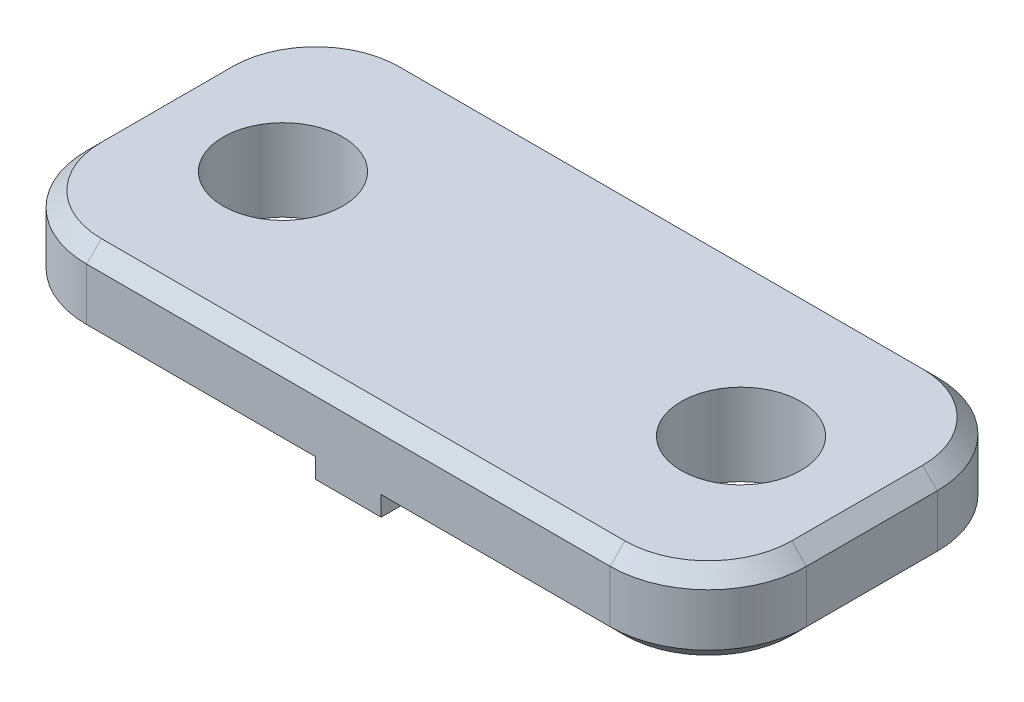
SolidWorks part; units mm, degrees
ref_plane "Front Plane" through (0, 0, 0) normal (0, 0, 1) x (1, 0, 0)
ref_plane "Top Plane" through (0, 0, 0) normal (0, 1, 0) x (1, 0, 0)
ref_plane "Right Plane" through (0, 0, 0) normal (1, 0, 0) x (0, 0, -1)
sketch "Sketch1" plane through (0, 0, 0) normal (0, 1, 0) x (1, 0, 0)
  line L1 (-11, -5) -> (11, -5)
  line L2 (-11, -5) -> (-11, 5)
  line L3 (-11, 5) -> (11, 5)
  line L4 (11, -5) -> (11, 5)
  line L5 (-11, -5) -> (11, 5) construction
  line L6 (-11, 5) -> (11, -5) construction
  point P0 (0, 0)
  dimension "D1" = 10
  dimension "D2" = 22
extrude "Boss-Extrude1" add sketch "Sketch1" along normal blind 2.5
hole_wizard "#6 Clearance Hole1" positions "Sketch2" profile "Sketch3" hole size "#6" standard "ANSI Inch" end condition through all
sketch "Sketch2" plane through (0, 2.5, 0) normal (0, 1, 0) x (1, 0, 0)
  line L0 (0, -55) -> (0, 55) construction
  point P0 (7, 0)
  point P5 (-7, 0)
  dimension "D1" = 7
sketch "Sketch3" plane through (7, 2.5, 0) normal (1, 0, 0) x (0, 0, 1)
  line L0 (0, 0) -> (0, 2.5)
  line L1 (0, 2.5) -> (1.8288, 2.5)
  line L2 (1.8288, 2.5) -> (1.8288, 0)
  line L5 (1.8288, 0) -> (0, 0)
  line L11 (0, -6.35) -> (0, 107.95) construction
  dimension "Thru Hole Dia." = 3.6576
  dimension "Thru Hole Depth" = 2.5
sketch "Sketch4" plane through (0, 0, 0) normal (0, -1, 0) x (1, 0, 0)
  line L0 (11, -5) -> (-11, -5) construction
  line L1 (-1, 5) -> (1, 5)
  line L2 (-1, 5) -> (-1, -5)
  line L3 (-1, -5) -> (1, -5)
  line L4 (1, 5) -> (1, -5)
  line L5 (-1, 5) -> (1, -5) construction
  line L6 (-1, -5) -> (1, 5) construction
  point P0 (0, 0)
  dimension "D1" = 2
extrude "Boss-Extrude2" add sketch "Sketch4" along normal blind 0.15
fillet "Fillet1" radius 3 4 edges at (11, 1.25, 5) (11, 1.25, -5) (-11, 1.25, -5) (-11, 1.25, 5)
chamfer "Chamfer1" distance 0.45 angle 45 18 edges at (4.5, 0, 5) (10.1213, 0, 4.1213) (11, 0, 0) (10.1213, 0, -4.1213) (4.5, 0, -5) (-4.5, 0, 5) (-4.5, 0, -5) (-10.1213, 0, -4.1213) (-11, 0, 0) (-10.1213, 0, 4.1213) (-10.1213, 2.5, -4.1213) (0, 2.5, -5) (10.1213, 2.5, -4.1213) (11, 2.5, 0) (10.1213, 2.5, 4.1213) (0, 2.5, 5) (-10.1213, 2.5, 4.1213) (-11, 2.5, 0)
